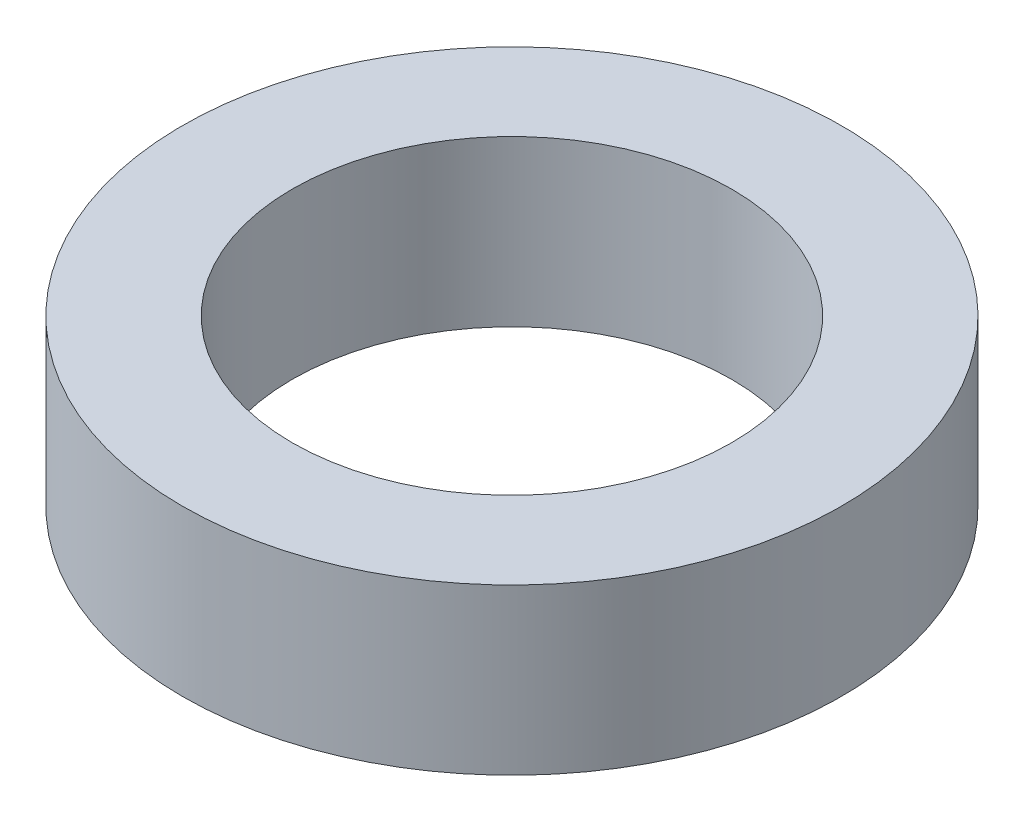
SolidWorks part; units mm, degrees
material "Nylon 101"
ref_plane "Front Plane" through (0, 0, 0) normal (0, 0, 1) x (1, 0, 0)
ref_plane "Top Plane" through (0, 0, 0) normal (0, 1, 0) x (1, 0, 0)
ref_plane "Right Plane" through (0, 0, 0) normal (1, 0, 0) x (0, 0, -1)
sketch "Sketch1" plane through (0, 0, 0) normal (0, 1, 0) x (1, 0, 0)
  circle A0 centre (0, 0) radius 9.525
  circle A1 centre (0, 0) radius 6.35
  dimension "D1" = 12.7
  dimension "D2" = 3.175
extrude "Boss-Extrude1" add sketch "Sketch1" along normal blind 4.7625
